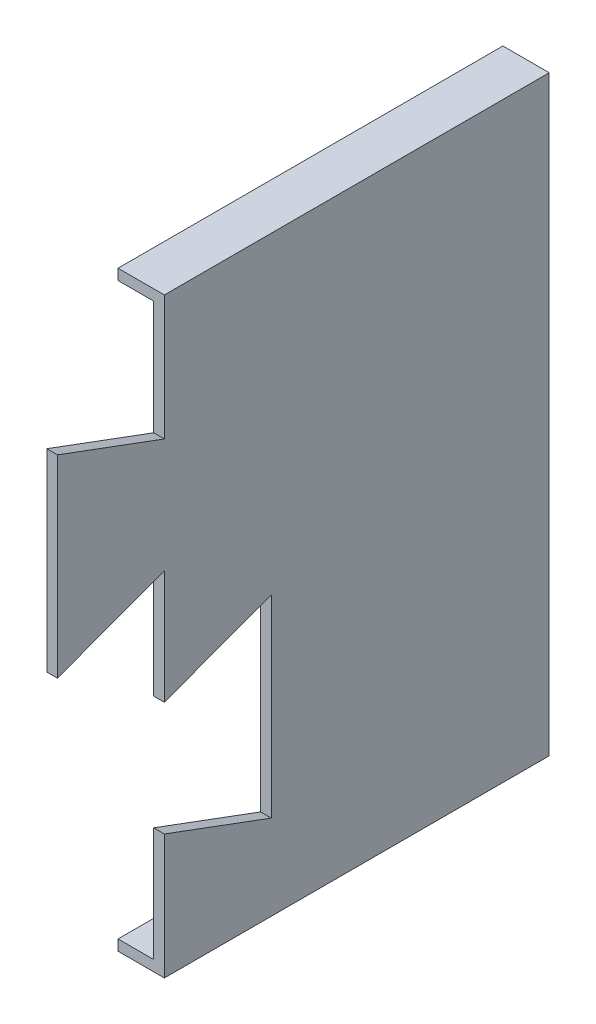
SolidWorks part; units mm, degrees
ref_plane "前基準面" through (0, 0, 0) normal (0, 0, 1) x (1, 0, 0)
ref_plane "上基準面" through (0, 0, 0) normal (0, 1, 0) x (1, 0, 0)
ref_plane "右基準面" through (0, 0, 0) normal (1, 0, 0) x (0, 0, -1)
sketch "草圖1" plane through (0, 0, 0) normal (0, 0, 1) x (1, 0, 0)
  line L1 (-21.6441, 19.0351) -> (-8.6441, 19.0351)
  line L2 (-21.6441, 19.0351) -> (-21.6441, -140.9649)
  line L3 (-21.6441, -140.9649) -> (-8.6441, -140.9649)
  line L4 (-8.6441, 19.0351) -> (-8.6441, -140.9649)
  dimension "D1" = 13
  dimension "D2" = 160
extrude "填料-伸長1" add sketch "草圖1" along normal blind 3
sketch "草圖2" plane through (0, 0, 3) normal (0, 0, 1) x (1, 0, 0)
  line L0 (-21.6441, -140.9649) -> (-8.6441, -140.9649) construction
  line L1 (-8.6441, 19.0351) -> (-11.6441, 19.0351)
  line L2 (-8.6441, 19.0351) -> (-8.6441, -140.9649)
  line L3 (-8.6441, -140.9649) -> (-11.6441, -140.9649)
  line L4 (-11.6441, 19.0351) -> (-11.6441, -140.9649)
  dimension "D1" = 3
extrude "填料-伸長2" add sketch "草圖2" along normal blind 135
sketch "草圖3" plane through (0, -140.9649, 0) normal (0, -1, 0) x (1, 0, 0)
  line L1 (-21.6441, 0) -> (-8.6441, 0)
  line L2 (-21.6441, 0) -> (-21.6441, 138)
  line L3 (-21.6441, 138) -> (-8.6441, 138)
  line L4 (-8.6441, 0) -> (-8.6441, 138)
extrude "填料-伸長3" add sketch "草圖3" along normal blind 3
sketch "草圖4" plane through (0, 19.0351, 0) normal (0, 1, 0) x (1, 0, 0)
  line L1 (-21.6441, 0) -> (-8.6441, 0)
  line L2 (-21.6441, 0) -> (-21.6441, -138)
  line L3 (-21.6441, -138) -> (-8.6441, -138)
  line L4 (-8.6441, 0) -> (-8.6441, -138)
extrude "填料-伸長4" add sketch "草圖4" along normal blind 3
sketch "草圖5" plane through (-8.6441, 0, 0) normal (1, 0, 0) x (0, 0, -1)
  line L0 (-108, -44.9649) -> (-138, -56.1004)
  line L1 (-138, 22.0351) -> (0, 22.0351) construction
  line L2 (-108, 22.0351) -> (-108, -12.9649)
  line L3 (-108, -76.9649) -> (-108, -44.9649)
  line L4 (-138, -56.1004) -> (-138, -1.8294)
  line L5 (-138, -143.9649) -> (-138, 22.0351) construction
  line L6 (-138, -1.8294) -> (-108, -12.9649)
  line L7 (-108, -108.9649) -> (-77.9998, -120.0999)
  line L8 (-77.9998, -120.0999) -> (-77.9998, -65.8299)
  line L9 (-77.9998, -65.8299) -> (-108, -76.9649)
  line L10 (-108, -143.9649) -> (-138, -143.9649)
  line L11 (-108, -108.9649) -> (-108, -143.9649)
  line L12 (0, -143.9649) -> (-138, -143.9649) construction
  line L13 (-138, -143.9649) -> (-138, -56.1004)
  line L14 (-138, -1.8294) -> (-138, 22.0351)
  line L15 (-138, 22.0351) -> (-108, 22.0351)
  line M16 (0, 22.0351) -> (-138, 22.0351)
  line M17 (-138, 22.0351) -> (-138, -143.9649)
  line M18 (-138, -143.9649) -> (0, -143.9649)
  dimension "D1" = 35
  dimension "D2" = 35
  dimension "D3" = 32
  dimension "D4" = 30
  dimension "D5" = 30
  dimension "D6" = 30
  dimension "D7" = 32
  dimension "D8" = 32
  dimension "D9" = 32
  dimension "D10" = 32
  dimension "D11" = 32
  dimension "D12" = 54.27
extrude "除料-伸長1" cut sketch "草圖5" against normal through all contours L11 L7 L8 L9 L3 L0 M17 M18 | L6 L2 M17 M16
